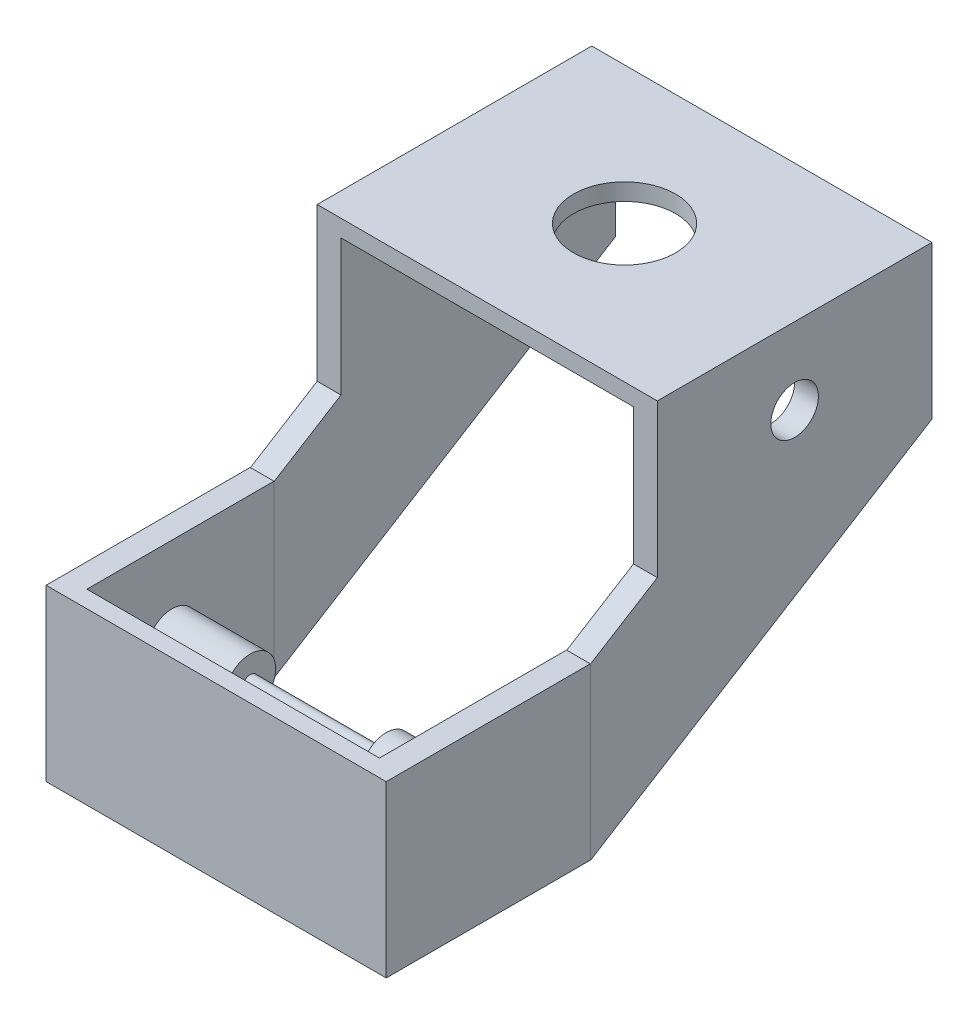
SolidWorks part; units mm, degrees
ref_plane "Front Plane" through (0, 0, 0) normal (0, 0, 1) x (1, 0, 0)
ref_plane "Top Plane" through (0, 0, 0) normal (0, 1, 0) x (1, 0, 0)
ref_plane "Right Plane" through (0, 0, 0) normal (1, 0, 0) x (0, 0, -1)
sketch "Sketch1" plane through (0, 0, 0) normal (0, 0, 1) x (1, 0, 0)
  line L1 (-48.5714, 40.5357) -> (51.4286, 40.5357)
  line L2 (-48.5714, 40.5357) -> (-48.5714, -9.4643)
  line L3 (-48.5714, -9.4643) -> (51.4286, -9.4643)
  line L4 (51.4286, 40.5357) -> (51.4286, -9.4643)
  dimension "D1" = 50
  dimension "D2" = 100
extrude "Boss-Extrude1" add sketch "Sketch1" along normal blind 5
sketch "Sketch2" plane through (0, 0, 0) normal (0, 0, 1) x (1, 0, 0)
  line L0 (-48.5714, -9.4643) -> (51.4286, -9.4643) construction
  line L1 (51.4286, 40.5357) -> (44.4286, 40.5357)
  line L2 (51.4286, 40.5357) -> (51.4286, -9.4643)
  line L3 (51.4286, -9.4643) -> (44.4286, -9.4643)
  line L4 (44.4286, 40.5357) -> (44.4286, -9.4643)
  line L6 (-48.5714, 40.5357) -> (-41.5714, 40.5357)
  line L7 (-48.5714, 40.5357) -> (-48.5714, -9.4643)
  line L8 (-48.5714, -9.4643) -> (-41.5714, -9.4643)
  line L9 (-41.5714, 40.5357) -> (-41.5714, -9.4643)
  dimension "D1" = 7
  dimension "D2" = 7
extrude "Boss-Extrude2" add sketch "Sketch2" against normal blind 55
ref_plane "Plane1" through (44.5, 0, 0) normal (1, 0, 0) x (0, 0, -1)
sketch "Sketch3" plane through (44.5, 0, 0) normal (1, 0, 0) x (0, 0, -1)
  line L0 (55, 40.5357) -> (74.6335, 52.6963)
  line L1 (55, -9.4643) -> (155.3597, 52.6963)
  line L2 (74.6335, 52.6963) -> (155.3597, 52.6963)
  line L3 (55, 40.5357) -> (55, -9.4643)
  dimension "D1" = 118.0508
  dimension "D2" = 19.6335
extrude "Boss-Extrude3" add sketch "Sketch3" along normal blind 7
ref_plane "Plane2" through (-41.5, 0, 0) normal (-1, 0, 0) x (0, 0, 1)
sketch "Sketch11" plane through (-41.5, 0, 0) normal (-1, 0, 0) x (0, 0, 1)
  line L0 (-55, -9.4643) -> (-55, 40.5357)
  line L1 (-55, 40.5357) -> (-74.6335, 52.6963)
  line L2 (-74.6335, 52.6963) -> (-155.3597, 52.6963)
  line L3 (-155.3597, 52.6963) -> (-55, -9.4643)
extrude "Boss-Extrude8" add sketch "Sketch11" along normal blind 7
sketch "Sketch14" plane through (-41.5, 0, 0) normal (-1, 0, 0) x (0, 0, 1)
  line L0 (-74.6335, 52.6963) -> (-74.6335, 92.6963)
  line L1 (-74.6335, 92.6963) -> (-155.3597, 92.6963)
  line L2 (-155.3597, 92.6963) -> (-155.3597, 52.6963)
  line L3 (-155.3597, 52.6963) -> (-74.6335, 52.6963)
  dimension "D1" = 40
extrude "Boss-Extrude11" add sketch "Sketch14" along normal blind 7
sketch "Sketch15" plane through (44.5, 0, 0) normal (1, 0, 0) x (0, 0, -1)
  line L0 (74.6335, 52.6963) -> (74.6335, 92.6963)
  line L1 (74.6335, 92.6963) -> (155.3597, 92.6963)
  line L2 (155.3597, 92.6963) -> (155.3597, 52.6963)
  line L3 (155.3597, 52.6963) -> (74.6335, 52.6963)
extrude "Boss-Extrude12" add sketch "Sketch15" along normal blind 7
ref_plane "Plane6" through (0, 119, 0) normal (0, 1, 0) x (1, 0, 0)
ref_plane "Plane7" through (0, 40, 0) normal (0, 1, 0) x (1, 0, 0)
sketch "Sketch24" plane through (0, 92.6963, 0) normal (0, 1, 0) x (1, 0, 0)
  line L1 (-48.5, 155.3597) -> (51.5, 155.3597)
  line L2 (-48.5, 155.3597) -> (-48.5, 74.6335)
  line L3 (-48.5, 74.6335) -> (51.5, 74.6335)
  line L4 (51.5, 155.3597) -> (51.5, 74.6335)
extrude "Boss-Extrude21" add sketch "Sketch24" along normal blind 5
sketch "Sketch25" plane through (-48.5, 0, 0) normal (-1, 0, 0) x (0, 0, 1)
  line L0 (-155.3597, 75.1963) -> (-74.6335, 75.1963) construction
  line L1 (-155.3597, 97.6963) -> (-155.3597, 52.6963) construction
  line L2 (-74.6335, 52.6963) -> (-74.6335, 97.6963) construction
  circle A0 centre (-114.9966, 75.1963) radius 7
  dimension "D1" = 14
extrude "Cut-Extrude5" cut sketch "Sketch25" against normal through all
sketch "Sketch26" plane through (0, 92.6963, 0) normal (0, -1, 0) x (1, 0, 0)
  line L0 (0, 0) -> (0, -171.2483) construction
  line L1 (-41.5, -114.9966) -> (44.5, -114.9966) construction
  line L2 (-41.5, -74.6335) -> (-41.5, -155.3597) construction
  line L3 (44.5, -155.3597) -> (44.5, -74.6335) construction
  circle A0 centre (1.5, -114.9966) radius 15
  dimension "D1" = 30
extrude "Cut-Extrude6" cut sketch "Sketch26" against normal blind 5
sketch "Sketch29" plane through (51.4286, 0, 0) normal (1, 0, 0) x (0, 0, -1)
  line L0 (55, 40.5357) -> (-5, -9.4643) construction
  line L1 (41.5119, 40.5357) -> (8.1802, -9.4643) construction
  line L2 (-5, 40.5357) -> (55, 40.5357) construction
  line L3 (-5, -9.4643) -> (55, -9.4643) construction
  line L4 (8.4881, -9.4643) -> (41.5119, 40.5357) construction
  line L5 (-5.5471, -0.1944) -> (27.4767, 49.8056)
  line L6 (22.5233, -18.7342) -> (55.5471, 31.2658)
  arc A0 (-5.5471, -0.1944) -> (22.5233, -18.7342) centre (8.4881, -9.4643) ccw
  arc A1 (55.5471, 31.2658) -> (27.4767, 49.8056) centre (41.5119, 40.5357) ccw
  point P4 (25, 15.5357)
  point P12 (25, 15.5357)
sketch "Sketch30" plane through (51.4286, 0, 0) normal (1, 0, 0) x (0, 0, -1)
  line L0 (-5, 40.5357) -> (55, -9.4643) construction
  line L1 (55, 40.5357) -> (-5, -9.4643) construction
  circle A0 centre (25, 15.5357) radius 2.25
  dimension "D1" = 4.5
extrude "Boss-Extrude22" add sketch "Sketch30" against normal through all
sketch "Sketch31" plane through (44.4286, 0, 0) normal (-1, 0, 0) x (0, 0, 1)
  line L0 (5, -9.4643) -> (-55, 40.5357) construction
sketch "Sketch32" plane through (44.4286, 0, 0) normal (-1, 0, 0) x (0, 0, 1)
  line L0 (5, 40.5357) -> (-55, -9.4643) construction
  line L1 (-55, 40.5357) -> (-55, -9.4643) construction
  line L2 (-155.3597, 52.6963) -> (-55, -9.4643) construction
  circle A0 centre (-25, 15.5357) radius 7.5
  dimension "D1" = 15
extrude "Boss-Extrude23" add sketch "Sketch32" along normal blind 23
sketch "Sketch33" plane through (-41.5714, 0, 0) normal (1, 0, 0) x (0, 0, -1)
  line L0 (-5, 40.5357) -> (55, -9.4643) construction
  circle A0 centre (25, 15.5357) radius 7.5
  dimension "D1" = 15
extrude "Boss-Extrude24" add sketch "Sketch33" along normal blind 23
